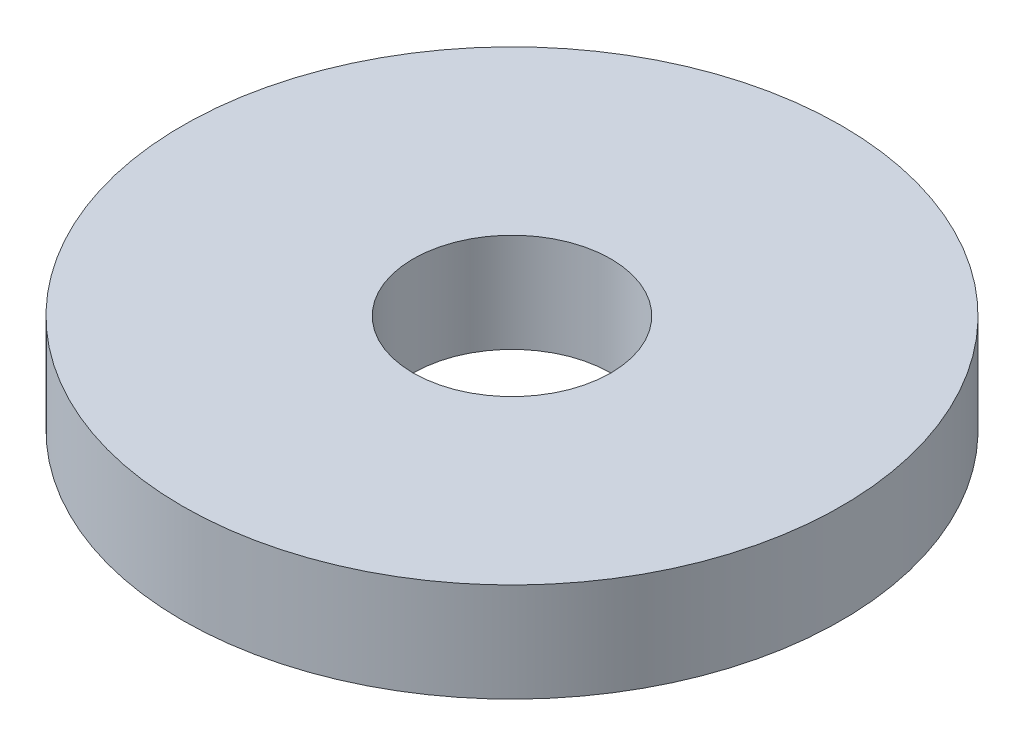
SolidWorks part; units mm, degrees
ref_plane "Front Plane" through (0, 0, 0) normal (0, 0, 1) x (1, 0, 0)
ref_plane "Top Plane" through (0, 0, 0) normal (0, 1, 0) x (1, 0, 0)
ref_plane "Right Plane" through (0, 0, 0) normal (1, 0, 0) x (0, 0, -1)
sketch "Sketch1" plane through (0, 0, 0) normal (0, 1, 0) x (1, 0, 0)
  circle A0 centre (0, 0) radius 1.5
  circle A1 centre (0, 0) radius 5
  dimension "D1" = 3
  dimension "D2" = 10
extrude "Boss-Extrude1" add sketch "Sketch1" along normal blind 1.5
